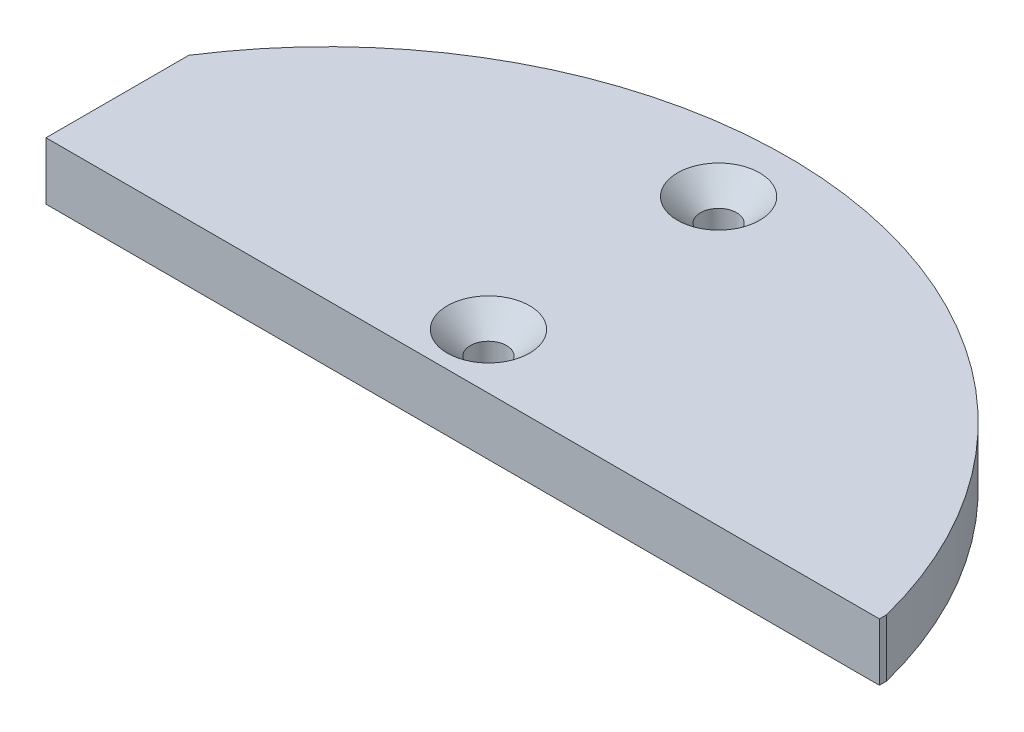
SolidWorks part; units mm, degrees
ref_plane "Front Plane" through (0, 0, 0) normal (0, 0, 1) x (1, 0, 0)
ref_plane "Top Plane" through (0, 0, 0) normal (0, 1, 0) x (1, 0, 0)
ref_plane "Right Plane" through (0, 0, 0) normal (1, 0, 0) x (0, 0, -1)
sketch "Sketch1" plane through (0, 0, 0) normal (0, 1, 0) x (1, 0, 0)
  line L0 (0, 17.78) -> (47.5869, 17.78) construction
  line L1 (0, 17.78) -> (-43, 17.78) construction
  line L2 (0, 17.78) -> (0, 11.43) construction
  line L3 (47.5869, 11.43) -> (49.4974, 11.43)
  line L4 (-43, 11.43) -> (47.5869, 11.43)
  line L5 (-43, 11.43) -> (-43, 50.8)
  line L6 (-43, 50.8) -> (47.5869, 50.8)
  line L7 (47.5869, 11.43) -> (47.5869, 50.8)
  line L8 (49.2434, 11.43) -> (49.2434, 50.546)
  line L9 (49.4974, 11.43) -> (-43, 11.43)
  line L10 (49.4974, 11.43) -> (49.4974, 50.8)
  line L11 (49.4974, 50.8) -> (-43, 50.8)
  line L12 (-43, 11.43) -> (-43, 50.8)
  line L13 (49.2434, 50.546) -> (-43, 50.546)
  line L14 (-42.746, 11.684) -> (47.5869, 11.684)
  line L15 (-42.746, 11.684) -> (-42.746, 50.8)
  line L16 (47.5869, 11.684) -> (49.2434, 11.684)
  circle A0 centre (0, 0) radius 50.8
  circle A1 centre (0, 17.78) radius 2
  circle A2 centre (0, 43.18) radius 2
  dimension "D1" = 101.6
  dimension "D2" = 17.78
  dimension "D4" = 4
  dimension "D5" = 4
  dimension "D3" = 25.4
  dimension "D6" = 6.35
  dimension "D7" = 43
  dimension "D8" = 0.254
  dimension "D9" = 0.254
extrude "Boss-Extrude1" add sketch "Sketch1" along normal blind 6.35 contours L7 A0 L13 L15 L14 A2 A1 | L8 A0 L7 L16 | L13 A0
chamfer "Chamfer1" distance 2.54 angle 45 2 edges at (0, 6.35, -15.78) (0, 6.35, -41.18)
sketch "Sketch2" plane through (0, 0, 0) normal (0, -1, 0) x (1, 0, 0)
  line L0 (47.3892, -13.2715) -> (-41.1585, -13.2715)
  line L1 (-41.1585, -13.2715) -> (-41.1585, -26.9787)
  line L2 (47.3892, -13.2715) -> (47.3892, -13.2715)
  line L3 (49.2434, -11.684) -> (-42.746, -11.684)
  line L4 (-42.746, -11.684) -> (-42.746, -27.4485)
  line L5 (49.2434, -12.479) -> (49.2434, -11.684)
  line L6 (49.2434, -11.684) -> (-42.746, -11.684)
  line L7 (-42.746, -11.684) -> (-42.746, -27.4485)
  line L8 (49.2434, -12.479) -> (49.2434, -11.684)
  arc A0 (-41.1585, -26.9787) -> (47.3892, -13.2715) centre (0, 0) ccw
  arc A1 (-42.746, -27.4485) -> (49.2434, -12.479) centre (0, 0) ccw
  arc A2 (-42.746, -27.4485) -> (49.2434, -12.479) centre (0, 0) ccw
  circle A3 centre (0, -17.78) radius 2
  circle A4 centre (0, -17.78) radius 2
  circle A5 centre (0, -43.18) radius 2
  circle A6 centre (0, -43.18) radius 2
  circle A7 centre (0, -17.78) radius 4
  circle A8 centre (0, -43.18) radius 4
  circle A9 centre (-5.4505, -15.2715) radius 2
  circle A10 centre (5.4505, -15.2715) radius 2
  circle A11 centre (4.6401, -46.9839) radius 2
  circle A12 centre (-4.6401, -46.9839) radius 2
  dimension "D6" = 4
  dimension "D7" = 4
  dimension "D8" = 4
  dimension "D9" = 4
  dimension "D1" = 0
  dimension "D2" = 0
  dimension "D3" = 0
  dimension "D4" = 1.5875
  dimension "D5" = 2
extrude "Cut-Extrude1" cut sketch "Sketch2" against normal offset from surface (4.7625 mm away) 1.5875 contours A10 A7 A9 L0 L1 A0 A8 | A9 | A10 | A12 | A11
fillet "Fillet1" radius 4 3 edges at (47.3892, 2.3813, -13.2715) (-41.1585, 2.3813, -26.9787) (-41.1585, 2.3813, -13.2715)
fillet "Fillet2" radius 2 14 edges at (-3.7664, 4.7625, -14.1927) (0, 4.7625, -21.78) (3.7664, 4.7625, -14.1927) (23.617, 4.7625, -13.2715) (45.1086, 4.7625, -15.048) (29.3355, 4.7625, -39.5132) (2.8766, 4.7625, -47.9274) (0, 4.7625, -39.18) (-2.8766, 4.7625, -47.9274) (-24.9446, 4.7625, -42.4221) (-40.9762, 4.7625, -26.9506) (-41.1585, 4.7625, -21.5142) (-39.9869, 4.7625, -14.4431) (-21.3045, 4.7625, -13.2715)
